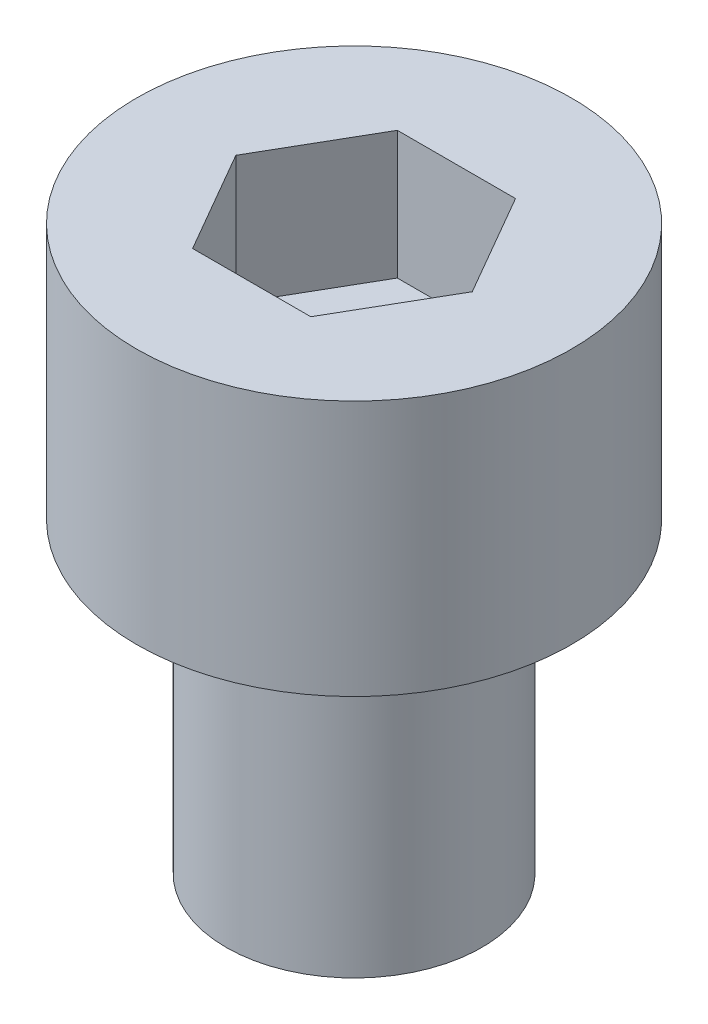
SolidWorks part; units mm, degrees
material "AISI 304"
ref_plane "前视基准面" through (0, 0, 0) normal (0, 0, 1) x (1, 0, 0)
ref_plane "上视基准面" through (0, 0, 0) normal (0, 1, 0) x (1, 0, 0)
ref_plane "右视基准面" through (0, 0, 0) normal (1, 0, 0) x (0, 0, -1)
sketch "草图1" plane through (0, 0, 0) normal (0, 1, 0) x (1, 0, 0)
  circle A0 centre (0, 0) radius 4.25
  dimension "D1" = 8.5
extrude "凸台-拉伸1" add sketch "草图1" along normal blind 5
sketch "草图2" plane through (0, 5, 0) normal (0, 1, 0) x (1, 0, 0)
  line L1 (2.3094, 0) -> (1.1547, 2)
  line L2 (1.1547, 2) -> (-1.1547, 2)
  line L3 (-1.1547, 2) -> (-2.3094, 0)
  line L4 (-2.3094, 0) -> (-1.1547, -2)
  line L5 (-1.1547, -2) -> (1.1547, -2)
  line L6 (1.1547, -2) -> (2.3094, 0)
  circle A0 centre (0, 0) radius 2 construction
  dimension "D1" = 4
extrude "切除-拉伸1" cut sketch "草图2" against normal blind 2.5
sketch "草图3" plane through (0, 0, 0) normal (0, -1, 0) x (1, 0, 0)
  circle A0 centre (0, 0) radius 2.5
  dimension "D1" = 5
extrude "凸台-拉伸2" add sketch "草图3" along normal blind 6
